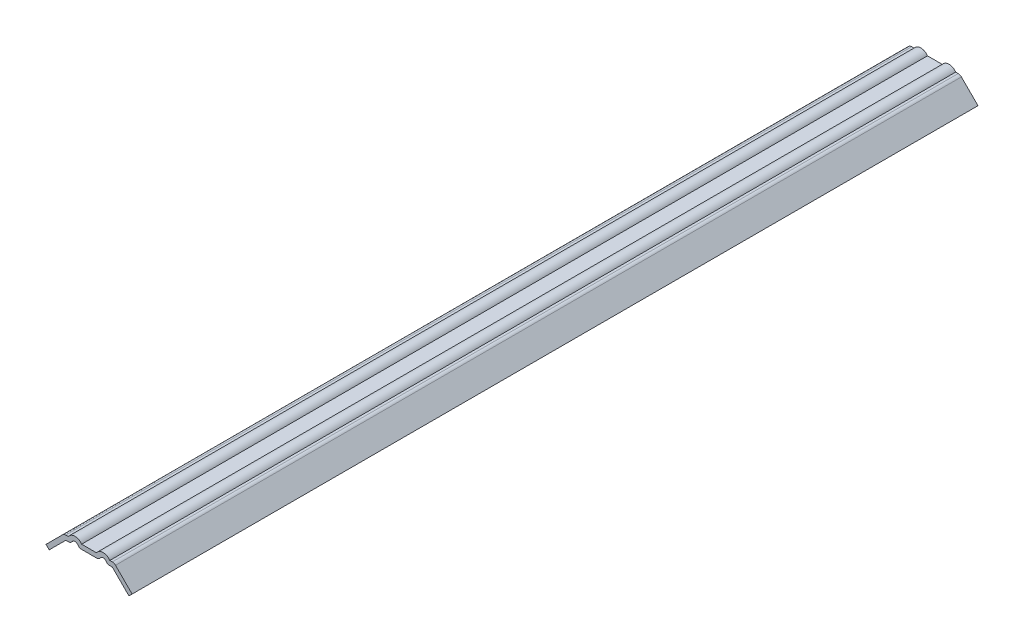
SolidWorks part; units mm, degrees
ref_plane "Front Plane" through (0, 0, 0) normal (0, 0, 1) x (1, 0, 0)
ref_plane "Top Plane" through (0, 0, 0) normal (0, 1, 0) x (1, 0, 0)
ref_plane "Right Plane" through (0, 0, 0) normal (1, 0, 0) x (0, 0, -1)
sketch "Sketch1" plane through (0, 0, 0) normal (0, 0, 1) x (1, 0, 0)
  line L0 (0, 0) -> (0, 38.1661) construction
  line L1 (0, 38.1661) -> (-7.1438, 38.1661)
  line L2 (-11.9062, 38.1661) -> (-15.7154, 38.1661)
  line L3 (-15.7154, 38.1661) -> (-26.9408, 26.9408)
  line L4 (-26.9408, 26.9408) -> (0, 0) construction
  arc A0 (-7.1438, 38.1661) -> (-11.9062, 38.1661) centre (-9.525, 38.1661) ccw
  point P6 (-8.5121, 16.7016)
  point P9 (-1.7759, 16.1512)
  point P10 (-11.9062, 17.5141)
  point P11 (-13.7386, 16.2875)
  point P12 (-14.8243, 14.8243)
  point P13 (-26.9408, 26.9408)
  point P14 (-18.9339, 33.1819)
  point P15 (-22.1509, 34.1124)
  point P16 (0, 0)
  point P17 (-17.643, 36.2386)
  point P18 (-16.1794, 37.7021)
  dimension "D1" = 2.3813
  dimension "D2" = 45
  dimension "D3" = 9.525
  dimension "D4" = 38.1
  dimension "D5" = 15.875
extrude "Extrude-Thin1" add sketch "Sketch1" against normal blind 571.5 thin
fillet "Fillet1" radius 3.048 3 edges at (-7.1438, 38.1661, -285.75) (-11.9062, 38.1661, -285.75) (-16.978, 41.2141, -285.75)
mirror "Mirror1" about plane through (0, 41.2141, -571.5) normal (-1, 0, 0) of bodies 101
